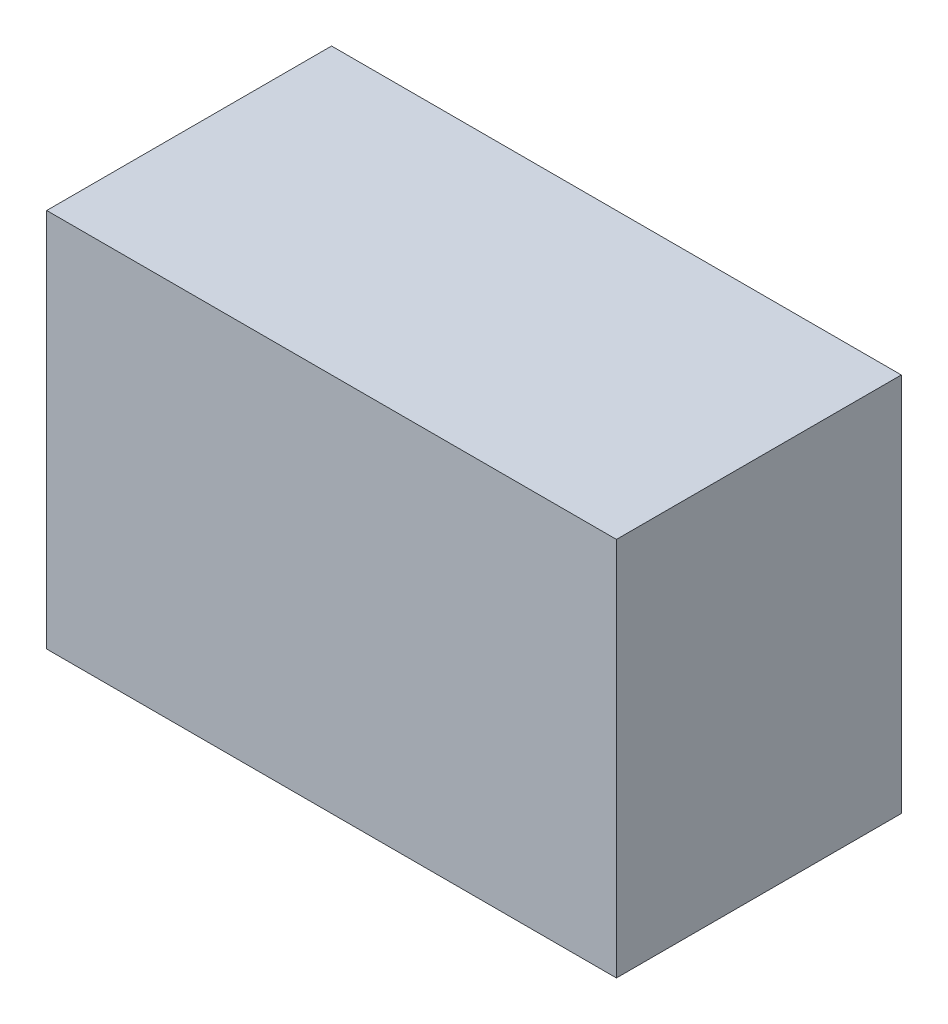
SolidWorks part; units mm, degrees
ref_plane "Front Plane" through (0, 0, 0) normal (0, 0, 1) x (1, 0, 0)
ref_plane "Top Plane" through (0, 0, 0) normal (0, 1, 0) x (1, 0, 0)
ref_plane "Right Plane" through (0, 0, 0) normal (1, 0, 0) x (0, 0, -1)
sketch "Layout" plane through (0, 0, 0) normal (0, 1, 0) x (1, 0, 0)
  line L0 (0, -6.35) -> (0, 3.175) construction
  line L1 (38.1, -19.05) -> (-38.1, -19.05)
  line L2 (38.1, -19.05) -> (38.1, 19.05)
  line L3 (38.1, 19.05) -> (-38.1, 19.05)
  line L4 (-38.1, -19.05) -> (-38.1, 19.05)
  line L5 (38.1, -19.05) -> (-38.1, 19.05) construction
  line L6 (38.1, 19.05) -> (-38.1, -19.05) construction
  line L7 (-19.05, -6.35) -> (-19.05, 3.175) construction
  line L8 (19.05, -6.35) -> (19.05, 3.175) construction
  line L9 (-12.7, 3.175) -> (-25.4, 3.175) construction
  line L10 (6.35, 3.175) -> (-6.35, 3.175) construction
  line L11 (25.4, 3.175) -> (12.7, 3.175) construction
  circle A0 centre (-19.05, -6.35) radius 3.9687
  circle A2 centre (0, -6.35) radius 3.9688
  circle A3 centre (19.05, -6.35) radius 3.9688
  circle A4 centre (-19.05, -6.35) radius 4.6789 construction
  circle A5 centre (0, -6.35) radius 5.5562 construction
  circle A6 centre (19.05, -6.35) radius 6.35 construction
  point P0 (0, 0)
  point P14 (-19.05, -6.35)
  point P21 (-19.05, 3.175)
  point P24 (0, 3.175)
  point P27 (19.05, 3.175)
  point P28 (-19.05, -6.35)
  point P29 (-19.05, -6.35)
  dimension "D3" = 7.9375
  dimension "D4" = 9.3579
  dimension "D5" = 11.1125
  dimension "D6" = 12.7
  dimension "D1" = 9.525
  dimension "D2" = 76.2
  dimension "D7" = 19.05
  dimension "D8" = 19.05
  dimension "D9" = 12.7
  dimension "D10" = 38.1
  dimension "D11" = 12.7
sketch "Sketch2" plane through (0, 0, 0) normal (0, 1, 0) x (1, 0, 0)
  line L3 (38.1, -19.05) -> (-38.1, -19.05) construction
  line L6 (38.1, -19.05) -> (38.1, 19.05) construction
  line L7 (38.1, 19.05) -> (-38.1, 19.05) construction
  line L8 (-38.1, -19.05) -> (-38.1, 19.05) construction
  line L9 (38.1, -19.05) -> (-38.1, -19.05)
  line L10 (38.1, -19.05) -> (38.1, 19.05)
  line L11 (38.1, 19.05) -> (-38.1, 19.05)
  line L12 (-38.1, -19.05) -> (-38.1, 19.05)
extrude "Boss-Extrude1" add sketch "Sketch2" along normal mid plane 50.8
ref_plane "Bottom flange" through (0, -5.08, 0) normal (0, -1, 0) x (-1, 0, 0)
sketch "Sketch4" plane through (0, -5.08, 0) normal (0, -1, 0) x (-1, 0, 0)
  line L0 (38.1, -19.05) -> (38.1, 19.05) construction
  line L1 (-38.1, -19.05) -> (38.1, -19.05) construction
  line L2 (-38.1, -19.05) -> (-38.1, 19.05) construction
  line L3 (-38.1, 19.05) -> (38.1, 19.05) construction
  line L4 (38.1, -19.05) -> (38.1, 19.05) construction
  line L5 (-38.1, -19.05) -> (38.1, -19.05) construction
  line L6 (-38.1, -19.05) -> (-38.1, 19.05) construction
  line L7 (-38.1, 19.05) -> (38.1, 19.05) construction
  line L8 (-38.1, -19.05) -> (38.1, 19.05) construction
  line L9 (34.925, -15.875) -> (-34.925, -15.875)
  line L10 (34.925, -15.875) -> (34.925, 15.875)
  line L11 (34.925, 15.875) -> (-34.925, 15.875)
  line L12 (-34.925, -15.875) -> (-34.925, 15.875)
  line L13 (34.925, -15.875) -> (-34.925, 15.875) construction
  line L14 (34.925, 15.875) -> (-34.925, -15.875) construction
  point P3 (0, 0)
  dimension "D1" = 3.175
  dimension "D2" = 3.175
extrude "Cut-Extrude1" cut sketch "Sketch4" along normal up to next
sketch "Sketch5" plane through (0, -5.08, 0) normal (0, -1, 0) x (-1, 0, 0)
  circle A0 centre (19.05, -6.35) radius 3.9687 construction
  circle A1 centre (0, -6.35) radius 3.9688 construction
  circle A2 centre (-19.05, -6.35) radius 3.9688 construction
  circle A3 centre (19.05, -6.35) radius 3.9687
  circle A4 centre (0, -6.35) radius 3.9688
  circle A5 centre (-19.05, -6.35) radius 3.9688
extrude "Cut-Extrude2" cut sketch "Sketch5" against normal blind 17.78
sketch "text" plane through (0, -5.08, 0) normal (0, -1, 0) x (-1, 0, 0)
  line L0 (12.7, 3.175) -> (25.4, 3.175) construction
  line L1 (-6.35, 3.175) -> (6.35, 3.175) construction
  line L2 (-25.4, 3.175) -> (-12.7, 3.175) construction
  line L3 (12.7, 3.175) -> (25.4, 3.175) construction
  line L4 (-6.35, 3.175) -> (6.35, 3.175) construction
  line L5 (-25.4, 3.175) -> (-12.7, 3.175) construction
  text T0 "#10" font "Arial Rounded MT Bold" height 4.572
  text T1 "1/4\"" font "Arial Rounded MT Bold" height 4.572
  text T2 "5/16\"" font "Arial Rounded MT Bold" height 4.572
extrude "Cut-Extrude3" cut sketch "text" against normal blind 2.032
